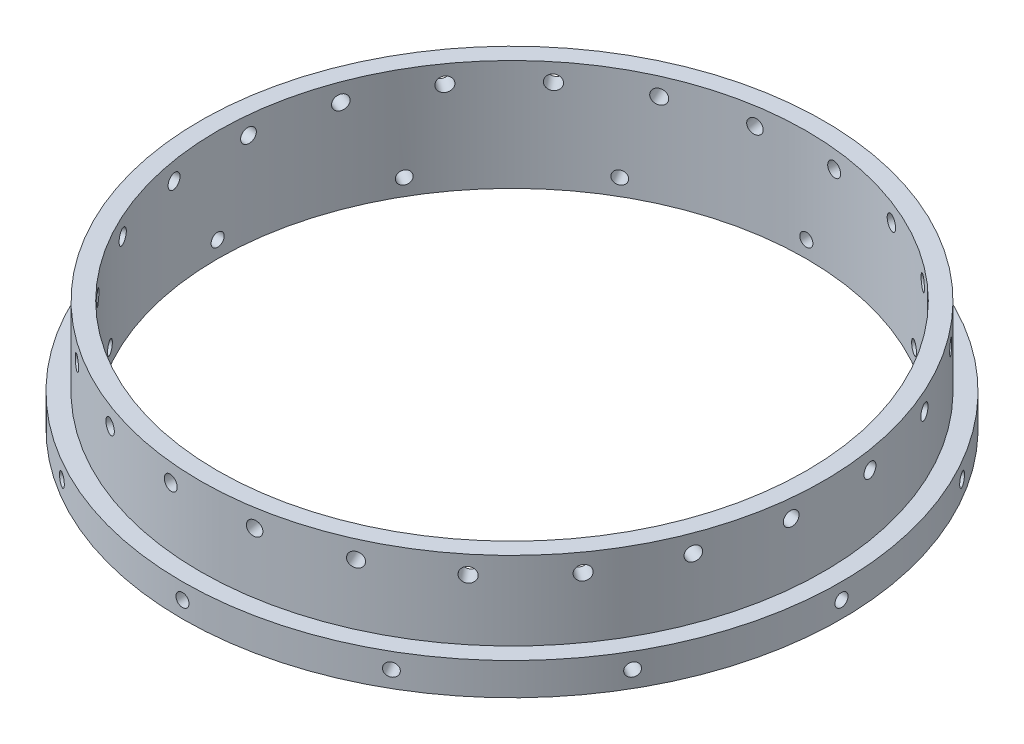
SolidWorks part; units mm, degrees
ref_plane "Front Plane" through (0, 0, 0) normal (0, 0, 1) x (1, 0, 0)
ref_plane "Top Plane" through (0, 0, 0) normal (0, 1, 0) x (1, 0, 0)
ref_plane "Right Plane" through (0, 0, 0) normal (1, 0, 0) x (0, 0, -1)
sketch "Sketch1" plane through (0, 0, 0) normal (0, 1, 0) x (1, 0, 0)
  circle A0 centre (0, 0) radius 75.565
  circle A1 centre (0, 0) radius 67.501
  dimension "D1" = 135.002
  dimension "D2" = 151.13
extrude "Boss-Extrude1" add sketch "Sketch1" along normal blind 25.4
hole_wizard "Tap Drill for M4x0.7 Tap1" positions "3DSketch1" profile "Sketch2" hole size "M4x0.7" standard "ANSI Metric"
sketch3d "3DSketch1"
  point P0 (31.0779, 21.2994, 68.8784)
sketch "Sketch2" plane through (31.0779, 21.2994, 68.8784) normal (0, 1, 0) x (0.9115, 0, -0.4113)
  line L0 (0, 0) -> (0, 153.0736)
  line L1 (0, 153.0736) -> (1.65, 153.0736)
  line L2 (1.65, 153.0736) -> (1.65, 0)
  line L5 (1.65, 0) -> (0, 0)
  line L11 (0, -6.35) -> (0, 107.95) construction
  dimension "Thru Hole Dia." = 3.3
  dimension "Thru Hole Depth" = 153.0736
pattern_circular "CirPattern1" count 24 every 15 about axis through (0, 25.4, 0) along (0, 1, 0) of "Tap Drill for M4x0.7 Tap1"
sketch "Sketch4" plane through (0, 0, 0) normal (1, 0, 0) x (0, 0, -1)
  line L0 (0, 0) -> (0, 3.7846) construction
  circle A0 centre (0, 3.7846) radius 1.5
extrude "Cut-Extrude1" cut sketch "Sketch4" against normal blind 113.03
pattern_circular "CirPattern2" count 12 every 30 about axis through (0, 0, 0) along (0, 1, 0) of "Cut-Extrude1"
sketch "Sketch7" plane through (0, 25.4, 0) normal (0, 1, 0) x (1, 0, 0)
  circle A0 centre (0, 0) radius 71.501
  circle A1 centre (0, 0) radius 75.565
  dimension "D1" = 143.002
extrude "Cut-Extrude2" cut sketch "Sketch7" against normal blind 18
